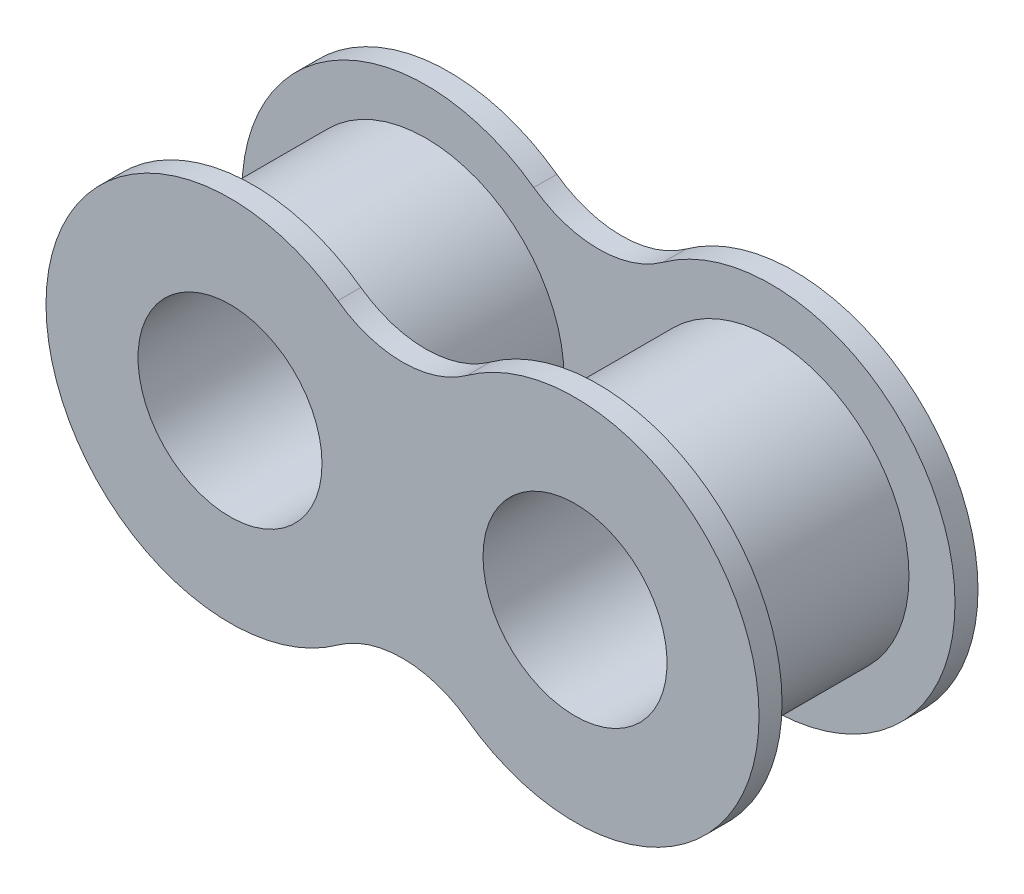
SolidWorks part; units mm, degrees
ref_plane "Front Plane" through (0, 0, 0) normal (0, 0, 1) x (1, 0, 0)
ref_plane "Top Plane" through (0, 0, 0) normal (0, 1, 0) x (1, 0, 0)
ref_plane "Right Plane" through (0, 0, 0) normal (1, 0, 0) x (0, 0, -1)
sketch "Sketch1" plane through (0, 0, 0) normal (0, 0, 1) x (1, 0, 0)
  line L0 (-13.4952, 0) -> (13.4952, 0) construction
  line L1 (0, -8.2181) -> (0, 8.2181) construction
  arc A0 (-1.7859, 4.1166) -> (-1.7859, -4.1166) centre (-4.7625, 0) ccw
  circle A1 centre (-4.7625, 0) radius 2.54
  arc A2 (1.7859, 4.1166) -> (1.7859, -4.1166) centre (4.7625, 0) cw
  circle A3 centre (4.7625, 0) radius 2.54
  arc A4 (-1.7859, 4.1166) -> (1.7859, 4.1166) centre (0, 6.5866) ccw
  arc A5 (-1.7859, -4.1166) -> (1.7859, -4.1166) centre (0, -6.5866) cw
  point P4 (0, 0)
  point P8 (0, 0)
  dimension "D1" = 5.08
  dimension "D2" = 10.16
  dimension "D4" = 3.048
  dimension "D3" = 9.525
extrude "Boss-Extrude1" add sketch "Sketch1" along normal blind 0.635
sketch "Sketch2" plane through (0, 0, 0.635) normal (0, 0, 1) x (1, 0, 0)
  circle A0 centre (-4.7625, 0) radius 2.54
  circle A1 centre (-4.7625, 0) radius 3.81
  circle A2 centre (-4.7625, 0) radius 2.54 construction
  point P3 (-4.3636, 0)
  point P6 (-4.7625, 0)
  dimension "D1" = 5.08
  dimension "D2" = 7.62
extrude "Boss-Extrude2" add sketch "Sketch2" along normal blind 4.7752
mirror "Mirror1" about plane through (0, 0, 0) normal (1, 0, 0) of "Boss-Extrude2"
ref_plane "Plane1" through (0, 0, 3.0226) normal (0, 0, 1) x (1, 0, 0)
mirror "Mirror2" about plane through (0, 0, 3.0226) normal (0, 0, 1) of "Boss-Extrude1"
sketch "Sketch3" plane through (0, 0, 3.0226) normal (0, 0, 1) x (1, 0, 0)
  line L0 (-190.5, 0) -> (190.5, 0) construction
  line L1 (-190.5, -25.9182) -> (-190.5, -51.8363) construction
  line L2 (190.5, -51.8363) -> (190.5, -25.9182) construction
  arc A0 (-190.5, 0) -> (-198.12, -50.6909) centre (-190.5, -25.9182) ccw construction
  arc A1 (198.12, -50.6909) -> (190.5, 0) centre (190.5, -25.9182) ccw construction
  spline S0 degree 3 poles (-198.12, -50.6909) (-133.2822, -70.6347) (-1.0529, -87.1691) (135.3881, -69.987) (198.12, -50.6909) knots 0 0 0 0 0.5 1 1 1 1 construction
  point P4 (0, 0)
  point P6 (-198.63, -50.5282)
  point P8 (230.7204, 18.6116)
  point P10 (16.3141, -72.9083)
  point P13 (0, -73.6105)
  point P14 (3.5141, -81.1095)
  point P16 (0, -79.1002)
  point P17 (0, -78.74)
  point P18 (0, -78.74)
  dimension "D2" = 51.8363
  dimension "D3" = 51.8363
  dimension "D6" = 78.74
  dimension "D1" = 381
  dimension "D4" = 7.62
  dimension "D5" = 7.62
  dimension "D7" = 78.74
